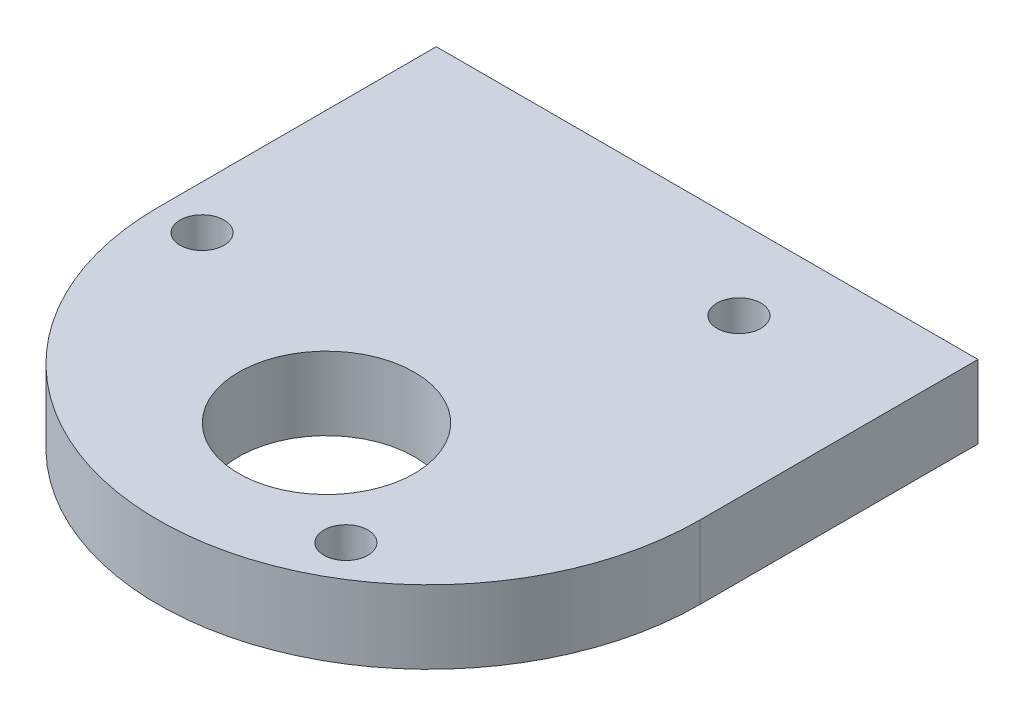
SolidWorks part; units mm, degrees
material "ｱｸﾘﾙ (中-上級の耐衝撃性)"
ref_plane "正面" through (0, 0, 0) normal (0, 0, 1) x (1, 0, 0)
ref_plane "平面" through (0, 0, 0) normal (0, 1, 0) x (1, 0, 0)
ref_plane "右側面" through (0, 0, 0) normal (1, 0, 0) x (0, 0, -1)
sketch "ｽｹｯﾁ1" plane through (0, 0, 0) normal (0, 0, 1) x (1, 0, 0)
  line L1 (-18.5, 2.5) -> (18.5, 2.5)
  line L2 (-18.5, 2.5) -> (-18.5, -2.5)
  line L3 (-18.5, -2.5) -> (18.5, -2.5)
  line L4 (18.5, 2.5) -> (18.5, -2.5)
  line L5 (-18.5, 2.5) -> (18.5, -2.5) construction
  line L6 (-18.5, -2.5) -> (18.5, 2.5) construction
  point P0 (0, 0)
  dimension "D1" = 5
  dimension "D2" = 37
extrude "ﾎﾞｽ - 押し出し1" add sketch "ｽｹｯﾁ1" along normal blind 19 contours L1 L4 L3 L2
sketch "ｽｹｯﾁ2" plane through (0, -2.5, 0) normal (0, -1, 0) x (1, 0, 0)
  line L0 (-18.5, 19) -> (18.5, 19) construction
  circle A0 centre (0, 19) radius 18.5
extrude "ﾎﾞｽ - 押し出し2" add sketch "ｽｹｯﾁ2" against normal blind 5
sketch "ｽｹｯﾁ3" plane through (0, -2.5, 0) normal (0, -1, 0) x (1, 0, 0)
  line L0 (-18.5, 19) -> (18.5, 19)
  line L1 (18.5, 19) -> (18.5, 0) construction
  line L2 (0, 19) -> (0, 26)
  line L3 (0, 19) -> (-15.5, 19)
  line L4 (0, 19) -> (7.75, 5.5766)
  line L5 (0, 19) -> (7.75, 32.4234)
  arc A0 (18.5, 19) -> (-18.5, 19) centre (0, 19) ccw construction
  circle A1 centre (0, 26) radius 6
  circle A2 centre (0, 19) radius 15.5
  circle A3 centre (-15.5, 19) radius 1.5
  circle A4 centre (7.75, 5.5766) radius 1.5
  circle A5 centre (7.75, 32.4234) radius 1.5
  dimension "D2" = 12
  dimension "D3" = 31
  dimension "D6" = 3
  dimension "D7" = 3
  dimension "D8" = 3
  dimension "D1" = 7
  dimension "D4" = 120
  dimension "D5" = 120
extrude "ｶｯﾄ - 押し出し1" cut sketch "ｽｹｯﾁ3" against normal blind 5 contours A1 | A5 | A3 | A4
sketch "ｽｹｯﾁ4" plane through (0, 0, 0) normal (0, 0, -1) x (-1, 0, 0)
  line L0 (0, 0) -> (-15, 0)
  line L1 (0, 0) -> (15, 0)
  dimension "D1" = 15
  dimension "D2" = 15
hole_wizard "M3x0.5 ねじ穴1" positions "ｽｹｯﾁ6" profile "ｽｹｯﾁ5" tap size "M3x0.5" standard "JIS"
sketch "ｽｹｯﾁ6" plane through (0, 0, 0) normal (0, 0, -1) x (-1, 0, 0)
  point P0 (15, 0)
  point P3 (-15, 0)
sketch "ｽｹｯﾁ5" plane through (-15, 0, 0) normal (1, 0, 0) x (0, 1, 0)
  line L0 (0, 0) -> (0, 10.7511)
  line L1 (0, 10.7511) -> (1.25, 10)
  line L2 (1.25, 10) -> (1.25, 0)
  line L5 (1.25, 0) -> (0, 0)
  line L10 (0, 10.7511) -> (-1.25, 10) construction
  line L11 (0, -6.35) -> (0, 107.95) construction
  dimension "ねじ下穴ﾄﾞﾘﾙ直径" = 2.5
  dimension "ねじ下穴ﾄﾞﾘﾙの深さ" = 10
  dimension "ﾄﾞﾘﾙ角度" = 118
cosmetic thread "穴のねじ山1" parameters "D1"=7, "D2"=3
cosmetic thread "穴のねじ山2" parameters "D1"=7, "D2"=3
